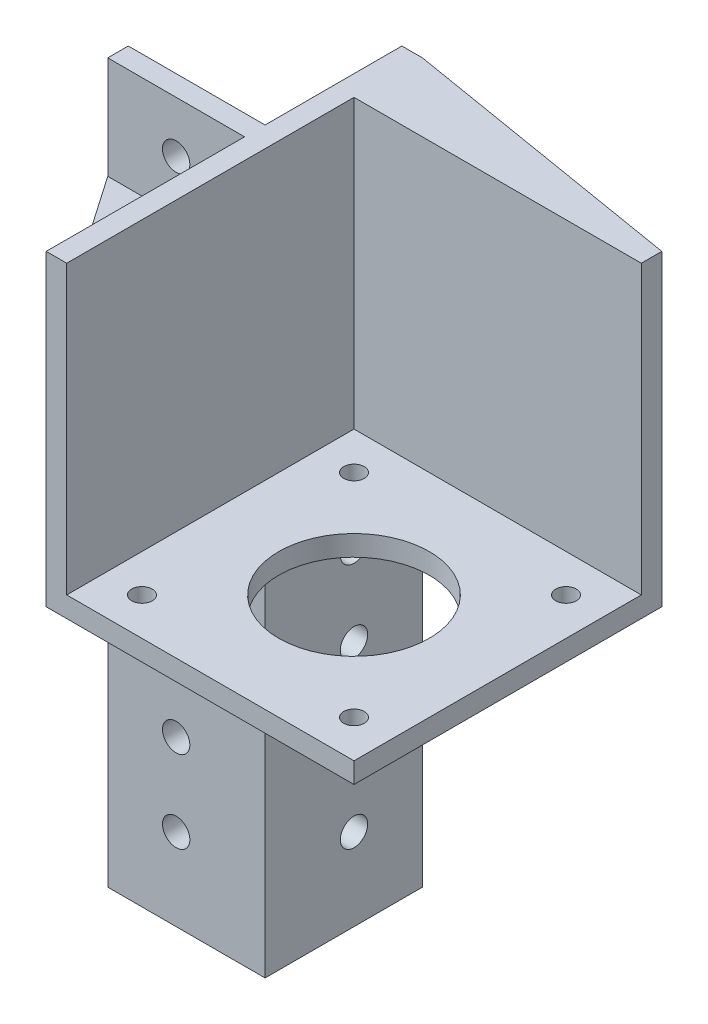
SolidWorks part; units mm, degrees
ref_plane "Front Plane" through (0, 0, 0) normal (0, 0, 1) x (1, 0, 0)
ref_plane "Top Plane" through (0, 0, 0) normal (0, 1, 0) x (1, 0, 0)
ref_plane "Right Plane" through (0, 0, 0) normal (1, 0, 0) x (0, 0, -1)
sketch "Sketch1" plane through (0, 0, 0) normal (0, 1, 0) x (1, 0, 0)
  line L0 (-21, 0) -> (0, 0) construction
  line L1 (-21, 21) -> (21, 21)
  line L2 (-21, 21) -> (-21, -21)
  line L3 (-21, -21) -> (21, -21)
  line L4 (21, 21) -> (21, -21)
  line L5 (-21, 21) -> (21, -21) construction
  line L6 (-21, -21) -> (21, 21) construction
  line L7 (0, 0) -> (0, -21) construction
  circle A0 centre (0, 0) radius 11
  circle A1 centre (-15.5, -15.5) radius 1.5
  circle A2 centre (15.5, -15.5) radius 1.5
  circle A3 centre (-15.5, 15.5) radius 1.5
  circle A4 centre (15.5, 15.5) radius 1.5
  point P0 (0, 0)
  dimension "D2" = 22
  dimension "D3" = 3
  dimension "D4" = 31
  dimension "D1" = 42
extrude "Boss-Extrude1" add sketch "Sketch1" along normal blind 3
sketch "Sketch2" plane through (-21, 0, 0) normal (-1, 0, 0) x (0, 0, 1)
  line L7 (-11, 0) -> (-11, -60)
  line L12 (-11, -60) -> (-31, -60)
  line L13 (-31, -60) -> (-31, 45)
  line L14 (-31, 45) -> (21, 45)
  line L15 (21, 45) -> (21, 0)
  line L16 (21, 0) -> (-11, 0)
  line L18 (-21, 3) -> (21, 3) construction
  line L19 (-21, 3) -> (-21, 0) construction
  point P5 (-4.1924, 0)
  dimension "D1" = 20
  dimension "D2" = 42
  dimension "D3" = 60
  dimension "D4" = 10
extrude "Boss-Extrude2" add sketch "Sketch2" along normal blind 3
sketch "Sketch4" plane through (0, 0, -21) normal (0, 0, -1) x (-1, 0, 0)
  line L1 (-21, 0) -> (21, 0)
  line L2 (-21, 0) -> (-21, 45)
  line L3 (-21, 45) -> (21, 45)
  line L4 (21, 0) -> (21, 45)
extrude "Boss-Extrude3" add sketch "Sketch4" along normal blind 3
sketch "Sketch5" plane through (0, 0, -11) normal (0, 0, 1) x (1, 0, 0)
  line L0 (-44, -60) -> (-21, -60)
  line L1 (-21, 0) -> (-24, 0)
  line L2 (-21, 0) -> (-21, -60)
  line L5 (-24, 45) -> (-44, 45)
  line L6 (-24, 45) -> (-24, 0)
  line L8 (-44, 45) -> (-44, -60)
  point P1 (0, 0)
  dimension "D1" = 20
extrude "Boss-Extrude4" add sketch "Sketch5" along normal blind 3
sketch "Sketch6" plane through (0, 0, 0) normal (0, -1, 0) x (1, 0, 0)
  line L0 (-24, 21) -> (-44, -8)
  line L1 (-44, -8) -> (-44, -11) construction
  line L2 (-44, -8) -> (-21, -8) construction
  line L3 (-44, -8) -> (-24, -8)
  line L4 (-24, -8) -> (-24, 21)
extrude "Boss-Extrude5" add sketch "Sketch6" against normal blind 30
sketch "Sketch7" plane through (0, 0, -8) normal (0, 0, 1) x (1, 0, 0)
  line L0 (-34, 45) -> (-34, 35.5) construction
  line L1 (-24, 45) -> (-44, 45) construction
  line L3 (-34, 37.5) -> (-44, 37.5) construction
  line L4 (-44, 45) -> (-44, 30) construction
  line L5 (-34, 35.5) -> (-34, 0) construction
  line L6 (-24, 0) -> (-44, 0) construction
  line L7 (-34, 0) -> (-34, -12) construction
  line L8 (-34, -12) -> (-34, -24) construction
  line L9 (-34, -24) -> (-34, -36) construction
  line L10 (-34, -36) -> (-34, -48) construction
  line L11 (-34, -48) -> (-34, -60) construction
  line L12 (-44, -60) -> (-21, -60) construction
  circle A0 centre (-34, 37.5) radius 2
  circle A1 centre (-34, -12) radius 2
  circle A2 centre (-34, -24) radius 2
  circle A3 centre (-34, -36) radius 2
  circle A4 centre (-34, -48) radius 2
  point P23 (-34, -11.2021)
  dimension "D1" = 4
extrude "Cut-Extrude1" cut sketch "Sketch7" against normal through all
sketch "Sketch8" plane through (0, 0, 0) normal (0, -1, 0) x (1, 0, 0)
  line L0 (21, -24) -> (-21, -31)
  line L1 (-21, -31) -> (-21, -24)
  line L2 (-21, -24) -> (21, -24)
extrude "Boss-Extrude6" add sketch "Sketch8" against normal up to surface (45 mm away) up to face at (-18.8333, 45, -12.3333)
sketch "Sketch9" plane through (-21, 0, 0) normal (1, 0, 0) x (0, 0, -1)
  line L0 (21, -60) -> (21, -48) construction
  line L1 (31, -60) -> (8, -60) construction
  line L2 (21, -48) -> (21, -36) construction
  line L3 (21, -36) -> (21, -24) construction
  line L4 (21, -24) -> (21, -12) construction
  line L5 (21, -12) -> (21, 0) construction
  line L6 (31, 0) -> (8, 0) construction
  line L7 (31, 0) -> (31, -60) construction
  circle A0 centre (21, -12) radius 2
  circle A1 centre (21, -24) radius 2
  circle A2 centre (21, -36) radius 2
  circle A3 centre (21, -48) radius 2
  dimension "D2" = 4
  dimension "D1" = 10
extrude "Cut-Extrude2" cut sketch "Sketch9" against normal through all
